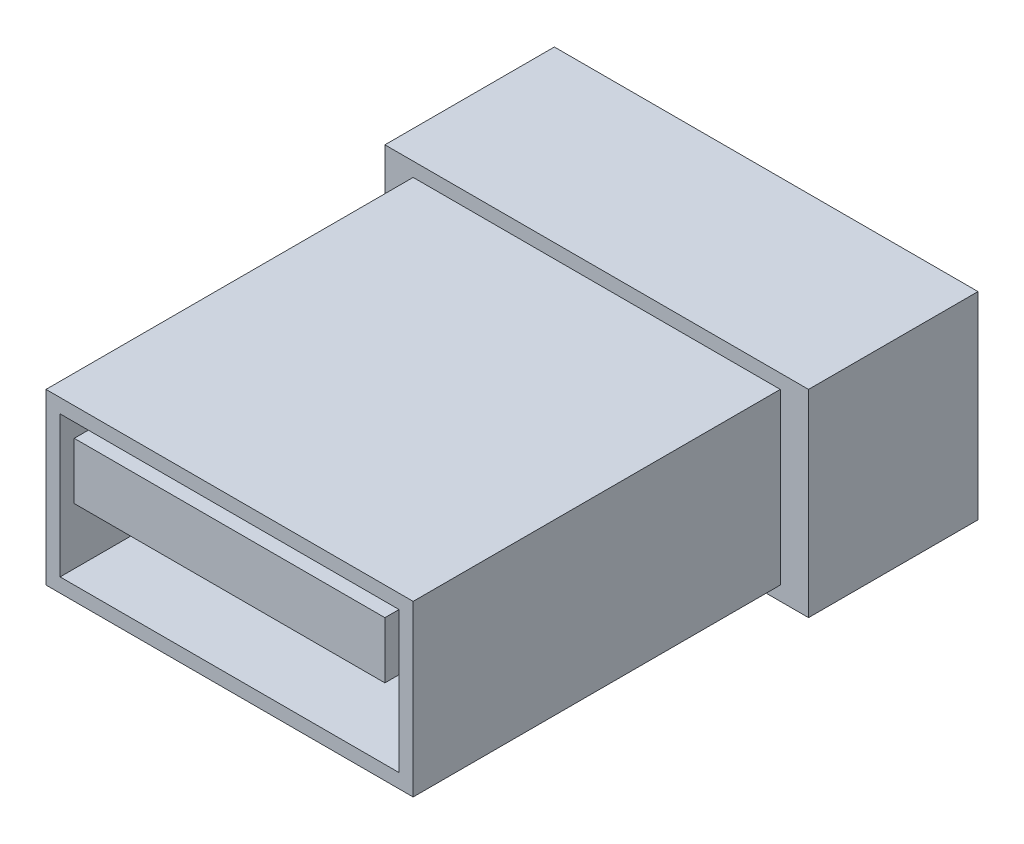
SolidWorks part; units mm, degrees
ref_plane "前视基准面" through (0, 0, 0) normal (0, 0, 1) x (1, 0, 0)
ref_plane "上视基准面" through (0, 0, 0) normal (0, 1, 0) x (1, 0, 0)
ref_plane "右视基准面" through (0, 0, 0) normal (1, 0, 0) x (0, 0, -1)
other "Configuration Table"
sketch "草图1" plane through (0, 0, 0) normal (1, 0, 0) x (0, 0, -1)
  line L1 (-13, 5) -> (0, 5)
  line L2 (-13, 5) -> (-13, 0)
  line L3 (-13, 0) -> (0, 0)
  line L4 (0, 5) -> (0, 0)
  line L5 (0, 6) -> (6, 6)
  line L6 (0, 6) -> (0, -1)
  line L7 (0, -1) -> (6, -1)
  line L8 (6, 6) -> (6, -1)
  point P9 (0, 0)
  dimension "D1" = 13
  dimension "D2" = 6
  dimension "D3" = 7
  dimension "D4" = 5
  dimension "D5" = 1
extrude "凸台-拉伸1" add sketch "草图1" along normal mid plane 12 contours L4 L1 L2 L3 | L6 L5 L8 L7
sketch "草图3" plane through (0, 0, 0) normal (1, 0, 0) x (0, 0, -1)
  line L1 (0, 6) -> (6, 6)
  line L2 (0, 6) -> (0, -1)
  line L3 (0, -1) -> (6, -1)
  line L4 (6, 6) -> (6, -1)
extrude "凸台-拉伸2" add sketch "草图3" along normal mid plane 15
sketch "草图4" plane through (0, 0, 13) normal (0, 0, 1) x (1, 0, 0)
  line L0 (0, 0) -> (0, 5) construction
  line L1 (6, 5) -> (-6, 5) construction
  line L2 (-6, 5) -> (-6, 0) construction
  line L3 (-5.5, 4.5) -> (5.5, 4.5)
  line L4 (-5.5, 4.5) -> (-5.5, 2.5)
  line L5 (-5.5, 2.5) -> (5.5, 2.5)
  line L6 (5.5, 4.5) -> (5.5, 2.5)
  line L7 (6, 5) -> (6, 0) construction
  line L8 (6, 5) -> (-6, 5) construction
  line L10 (-6, 5) -> (6, 5)
  line L11 (-6, 5) -> (-6, 0)
  line L12 (-6, 0) -> (6, 0)
  line L13 (6, 5) -> (6, 0)
  dimension "D1" = 0.5
  dimension "D2" = 0.5
  dimension "D3" = 0.5
  dimension "D4" = 2
extrude "切除-拉伸1" cut sketch "草图4" against normal up to surface (13 mm away) up to face at (0, 2.5, 0)
sketch "草图5" plane through (0, 0, 0) normal (0, 0, 1) x (1, 0, 0)
  line L0 (5.5, 4.5) -> (-5.5, 4.5) construction
  line L1 (-6, 5) -> (6, 5)
  line L2 (-6, 5) -> (-6, 0)
  line L3 (-6, 0) -> (6, 0)
  line L4 (6, 5) -> (6, 0)
  line L5 (5.5, 2.5) -> (5.5, 4.5) construction
  line L6 (-5.5, 4.5) -> (-5.5, 2.5) construction
  dimension "D1" = 0.5
  dimension "D2" = 0.5
  dimension "D3" = 0.5
  dimension "D4" = 5
extrude "拉伸-薄壁1" add sketch "草图5" along normal blind 13 thin thin type one direction wall 0.5
